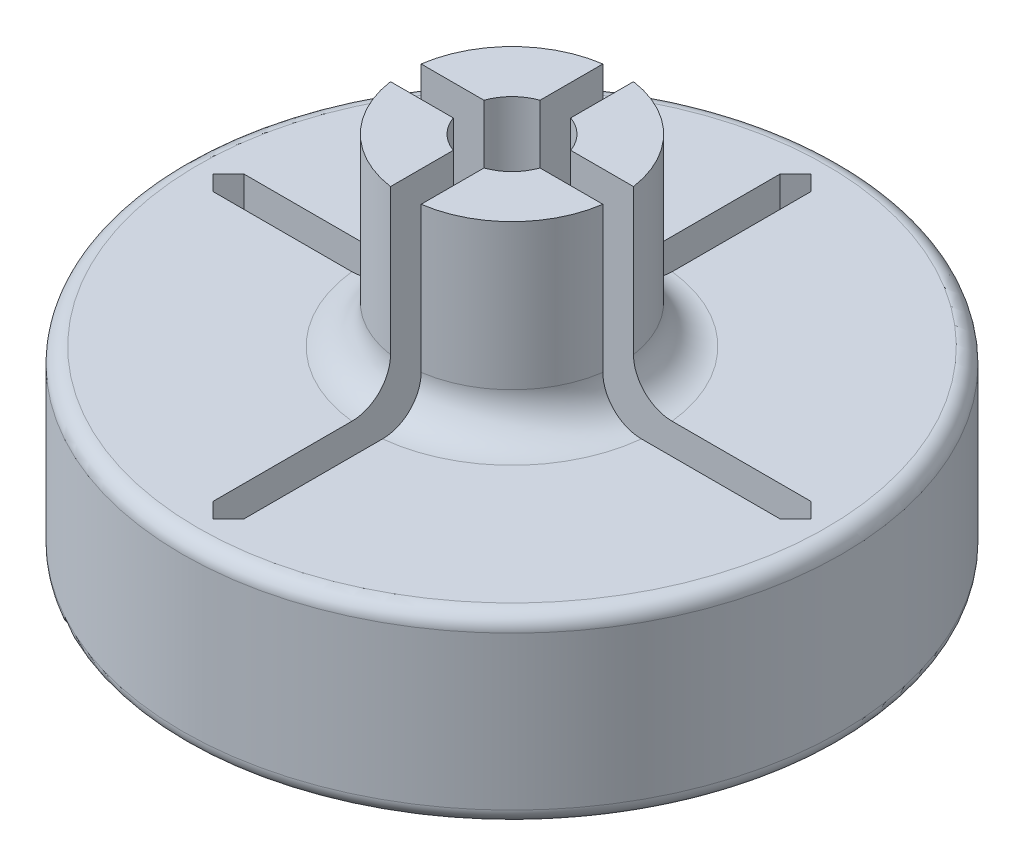
SolidWorks part; units mm, degrees
ref_plane "Front Plane" through (0, 0, 0) normal (0, 0, 1) x (1, 0, 0)
ref_plane "Top Plane" through (0, 0, 0) normal (0, 1, 0) x (1, 0, 0)
ref_plane "Right Plane" through (0, 0, 0) normal (1, 0, 0) x (0, 0, -1)
sketch "Sketch1" plane through (0, 0, 0) normal (0, 1, 0) x (1, 0, 0)
  circle A0 centre (0, 0) radius 9.75
  circle A1 centre (0, 0) radius 10.75
  dimension "D1" = 19.5
  dimension "D2" = 1
extrude "Boss-Extrude1" add sketch "Sketch1" along normal blind 1 contours A0 | A1 A0
sketch "Sketch2" plane through (0, 1, 0) normal (0, 1, 0) x (1, 0, 0)
  circle A0 centre (0, 0) radius 9.75
  circle A1 centre (0, 0) radius 10.75
  circle A2 centre (0, 0) radius 10.75 construction
  dimension "D1" = 1
extrude "Boss-Extrude2" add sketch "Sketch2" along normal blind 3.5
sketch "Sketch3" plane through (0, 4.5, 0) normal (0, 1, 0) x (1, 0, 0)
  circle A0 centre (0, 0) radius 10.75
  circle A1 centre (0, 0) radius 10.75 construction
extrude "Boss-Extrude3" add sketch "Sketch3" along normal blind 1.5
sketch "Sketch4" plane through (0, 6, 0) normal (0, 1, 0) x (1, 0, 0)
  line L0 (0, 0) -> (0, 9.75) construction
  line L1 (0, 9.75) -> (0, 10.75) construction
  line L2 (-0.5, 0.5) -> (-0.5, 9.25)
  line L3 (-0.5, 9.25) -> (0, 9.75)
  line L4 (0, 9.75) -> (0.5, 9.25)
  line L5 (0.5, 9.25) -> (0.5, 0.5)
  line L6 (0.5, 0.5) -> (9.25, 0.5)
  line L7 (9.25, -0.5) -> (0.5, -0.5)
  line L8 (9.75, 0) -> (9.25, -0.5)
  line L9 (9.25, 0.5) -> (9.75, 0)
  line L10 (0.5, -0.5) -> (0.5, -9.25)
  line L11 (-0.5, -9.25) -> (-0.5, -0.5)
  line L12 (0, -9.75) -> (-0.5, -9.25)
  line L13 (0.5, -9.25) -> (0, -9.75)
  line L14 (-0.5, -0.5) -> (-9.25, -0.5)
  line L15 (-9.25, 0.5) -> (-0.5, 0.5)
  line L16 (-9.75, 0) -> (-9.25, 0.5)
  line L17 (-9.25, -0.5) -> (-9.75, 0)
  line L18 (-0.5, 0.5) -> (0.5, 0.5) construction
  circle A0 centre (0, 0) radius 10.75 construction
  circle A1 centre (0, 0) radius 1.5
  point P0 (0, 0)
  point P30 (0, 0)
  dimension "D7" = 3
  dimension "D1" = 1
  dimension "D2" = 0.5
  dimension "D3" = 0.5
  dimension "D4" = 45
  dimension "D6" = 0.5
  dimension "D5" = 4
extrude "Cut-Extrude1" cut sketch "Sketch4" against normal blind 1 contours L17 L14 L11 L12 L13 L10 L7 L8 L9 L6 L5 L4 L3 L2 L15 L16 | A1 L15 L16 L17 L14 | A1 L7 L8 L9 L6 | A1 L5 L4 L3 L2 | A1 L11 L12 L13 L10 | L14 A1 L11 | L2 A1 L15 | L6 A1 L5 | L10 A1 L7
sketch "Sketch6" plane through (0, 6, 0) normal (0, 1, 0) x (1, 0, 0)
  line L0 (0.5, 1.4142) -> (0.5, 3.4641)
  line L1 (0.5, 9.25) -> (0.5, 1.4142) construction
  line L2 (1.4142, 0.5) -> (3.4641, 0.5)
  line L3 (1.4142, 0.5) -> (9.25, 0.5) construction
  line L4 (0.5, -1.4142) -> (0.5, -3.4641)
  line L5 (1.4142, -0.5) -> (3.4641, -0.5)
  line L6 (-1.4142, -0.5) -> (-3.4641, -0.5)
  line L7 (-0.5, -1.4142) -> (-0.5, -3.4641)
  line L8 (-0.5, 1.4142) -> (-0.5, 3.4641)
  line L9 (-1.4142, 0.5) -> (-3.4641, 0.5)
  arc A0 (0.5, 1.4142) -> (1.4142, 0.5) centre (0, 0) cw
  arc A1 (1.4142, 0.5) -> (0.5, 1.4142) centre (0, 0) ccw construction
  arc A2 (0.5, 3.4641) -> (3.4641, 0.5) centre (0, 0) cw
  arc A3 (3.4641, -0.5) -> (0.5, -3.4641) centre (0, 0) cw
  arc A4 (1.4142, -0.5) -> (0.5, -1.4142) centre (0, 0) cw
  arc A5 (-0.5, -3.4641) -> (-3.4641, -0.5) centre (0, 0) cw
  arc A6 (-0.5, -1.4142) -> (-1.4142, -0.5) centre (0, 0) cw
  arc A7 (-3.4641, 0.5) -> (-0.5, 3.4641) centre (0, 0) cw
  arc A8 (-1.4142, 0.5) -> (-0.5, 1.4142) centre (0, 0) cw
  point P30 (0, 0)
  dimension "D1" = 2
  dimension "D2" = 4
extrude "Boss-Extrude4" add sketch "Sketch6" along normal blind 6
fillet "Fillet1" radius 1.25 4 edges at (2.4749, 6, 2.4749) (2.4749, 6, -2.4749) (-2.4749, 6, -2.4749) (-2.4749, 6, 2.4749)
fillet "Fillet2" radius 0.5 2 edges at (0, 6, 10.75) (0, 0, 10.75)
